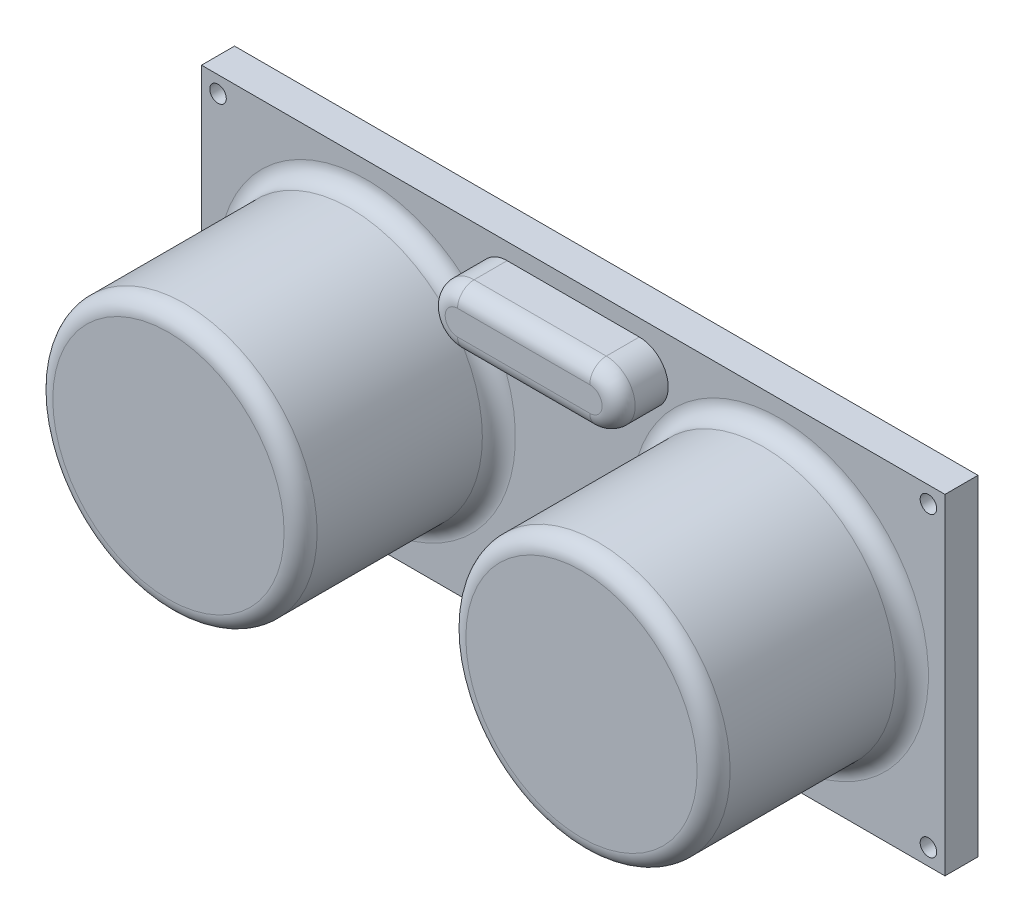
SolidWorks part; units mm, degrees
ref_plane "Alzado" through (0, 0, 0) normal (0, 0, 1) x (1, 0, 0)
ref_plane "Planta" through (0, 0, 0) normal (0, 1, 0) x (1, 0, 0)
ref_plane "Vista lateral" through (0, 0, 0) normal (1, 0, 0) x (0, 0, -1)
sketch "Croquis1" plane through (0, 0, 0) normal (0, 0, 1) x (1, 0, 0)
  line L1 (-22.5, -10) -> (22.5, -10)
  line L2 (-22.5, -10) -> (-22.5, 10)
  line L3 (-22.5, 10) -> (22.5, 10)
  line L4 (22.5, -10) -> (22.5, 10)
  line L5 (-22.5, -10) -> (22.5, 10) construction
  line L6 (-22.5, 10) -> (22.5, -10) construction
  point P0 (0, 0)
extrude "Saliente-Extruir1" add sketch "Croquis1" along normal blind 2
sketch "Croquis2" plane through (0, 0, 2) normal (0, 0, 1) x (1, 0, 0)
  line L0 (-22.5, 0) -> (22.5, 0) construction
  line L1 (-22.5, 10) -> (-22.5, -10) construction
  line L2 (22.5, -10) -> (22.5, 10) construction
  line L3 (22.5, 0) -> (20.5, 0) construction
  line L4 (20.5, 0) -> (12.5, 0) construction
  line L5 (0, 0) -> (0, 10) construction
  line L6 (22.5, 10) -> (-22.5, 10) construction
  circle A0 centre (12.5, 0) radius 8
  circle A1 centre (-12.5, 0) radius 8
extrude "Saliente-Extruir2" add sketch "Croquis2" along normal blind 12
fillet "Redondeo1" radius 1 4 edges at (-20.5, 0, 2) (-20.5, 0, 14) (4.5, 0, 2) (20.5, 0, 14)
sketch "Croquis3" plane through (0, 0, 2) normal (0, 0, 1) x (1, 0, 0)
  line L0 (0, 0) -> (0, 10) construction
  line L1 (22.5, 10) -> (-22.5, 10) construction
  line L2 (0, 10) -> (0, 9) construction
  line L3 (0, 9) -> (0, 5.5) construction
  line L4 (0, 5.5) -> (0, 7.25) construction
  line L5 (0, 7.25) -> (4, 7.25) construction
  line L6 (4, 7.25) -> (-4, 7.25) construction
  line L8 (4, 5.5) -> (-4, 5.5)
  line L9 (4, 9) -> (-4, 9)
  arc A0 (4, 5.5) -> (4, 9) centre (4, 7.25) ccw
  arc A1 (-4, 9) -> (-4, 5.5) centre (-4, 7.25) ccw
  point P12 (0, 7.25)
extrude "Saliente-Extruir3" add sketch "Croquis3" along normal blind 3
fillet "Redondeo2" radius 1 4 edges at (0, 5.5, 5) (-5.75, 7.25, 5) (0, 9, 5) (5.75, 7.25, 5)
sketch "Croquis4" plane through (0, 0, 2) normal (0, 0, 1) x (1, 0, 0)
  line L0 (0, 0) -> (0, 50000) construction
  line L1 (0, 0) -> (50000, 0) construction
  line L2 (22.5, 10) -> (22.5, 9) construction
  line L3 (22.5, -10) -> (22.5, 10) construction
  line L4 (22.5, 9) -> (21.5, 9) construction
  circle A0 centre (21.5, 9) radius 0.5
  circle A1 centre (21.5, -9) radius 0.5
  circle A2 centre (-21.5, -9) radius 0.5
  circle A3 centre (-21.5, 9) radius 0.5
extrude "Cortar-Extruir1" cut sketch "Croquis4" against normal through all
sketch "Croquis5" plane through (0, 0, 0) normal (0, 0, -1) x (-1, 0, 0)
  line L0 (0, 0) -> (0, -10) construction
  line L1 (22.5, -10) -> (-22.5, -10) construction
  line L2 (0, -10) -> (0, -7) construction
  line L3 (-5, -7) -> (5, -7) construction
  line L5 (5, -7) -> (-5, -7)
  line L6 (5, -7) -> (5, -10)
  line L7 (5, -10) -> (-5, -10)
  line L8 (-5, -7) -> (-5, -10)
  point P9 (0, -7)
extrude "Saliente-Extruir4" add sketch "Croquis5" along normal blind 2.54
chamfer "Chaflán1" distance 0.2 angle 45 4 edges at (-5, -10, -1.27) (-5, -7, -1.27) (5, -10, -1.27) (5, -7, -1.27)
sketch "Croquis6" plane through (0, 0, -2.54) normal (0, 0, -1) x (-1, 0, 0)
  line L0 (0, -7) -> (0, -10) construction
  line L1 (4.8, -7) -> (-4.8, -7) construction
  line L2 (-4.8, -10) -> (4.8, -10) construction
  line L3 (0, -10) -> (0, -8.5) construction
  line L4 (0, -8.5) -> (5, -8.5) construction
  line L5 (5, -9.8) -> (5, -7.2) construction
  line L6 (5, -8.5) -> (-5, -8.5) construction
  line L7 (-5, -7.2) -> (-5, -9.8) construction
  line L8 (-5, -8.5) -> (0, -8.5) construction
  line L9 (0, -8.5) -> (-2.5, -8.5) construction
  line L10 (-2.5, -8.5) -> (-5, -8.5) construction
  line L11 (-5, -8.5) -> (-3.75, -8.5) construction
  line L12 (-3.75, -8.5) -> (-1.25, -8.5) construction
  line L13 (5, -8.5) -> (0, -8.5) construction
  line L14 (0, -8.5) -> (2.5, -8.5) construction
  line L15 (2.5, -8.5) -> (1.25, -8.5) construction
  line L16 (1.25, -8.5) -> (2.5, -8.5) construction
  line L17 (2.5, -8.5) -> (5, -8.5) construction
  line L18 (5, -8.5) -> (3.75, -8.5) construction
  line L20 (-4.1, -8.85) -> (-3.4, -8.85)
  line L21 (-4.1, -8.85) -> (-4.1, -8.15)
  line L22 (-4.1, -8.15) -> (-3.4, -8.15)
  line L23 (-3.4, -8.85) -> (-3.4, -8.15)
  line L24 (-4.1, -8.85) -> (-3.4, -8.15) construction
  line L25 (-4.1, -8.15) -> (-3.4, -8.85) construction
  line L26 (-1.6, -8.85) -> (-0.9, -8.85)
  line L27 (-1.6, -8.85) -> (-1.6, -8.15)
  line L28 (-1.6, -8.15) -> (-0.9, -8.15)
  line L29 (-0.9, -8.85) -> (-0.9, -8.15)
  line L30 (-1.6, -8.85) -> (-0.9, -8.15) construction
  line L31 (-1.6, -8.15) -> (-0.9, -8.85) construction
  line L32 (0.9, -8.85) -> (1.6, -8.85)
  line L33 (0.9, -8.85) -> (0.9, -8.15)
  line L34 (0.9, -8.15) -> (1.6, -8.15)
  line L35 (1.6, -8.85) -> (1.6, -8.15)
  line L36 (0.9, -8.85) -> (1.6, -8.15) construction
  line L37 (0.9, -8.15) -> (1.6, -8.85) construction
  line L38 (3.4, -8.85) -> (4.1, -8.85)
  line L39 (3.4, -8.85) -> (3.4, -8.15)
  line L40 (3.4, -8.15) -> (4.1, -8.15)
  line L41 (4.1, -8.85) -> (4.1, -8.15)
  line L42 (3.4, -8.85) -> (4.1, -8.15) construction
  line L43 (3.4, -8.15) -> (4.1, -8.85) construction
extrude "Saliente-Extruir5" add sketch "Croquis6" along normal blind 1
sketch "Croquis7" plane through (0, 0, -3.54) normal (0, 0, -1) x (-1, 0, 0)
  line L0 (-4.1, -8.85) -> (4.1, -8.85) construction
  line L1 (-4.1, -8.85) -> (-4.1, -9.15) construction
  line L2 (-4.1, -9.15) -> (4.1, -9.15) construction
  line L4 (-4.1, -8.15) -> (-3.4, -8.15)
  line L5 (-4.1, -8.15) -> (-4.1, -8.85)
  line L6 (-4.1, -8.85) -> (-3.4, -8.85)
  line L7 (-3.4, -8.15) -> (-3.4, -8.85)
  line L8 (-1.6, -8.15) -> (-0.9, -8.15)
  line L9 (-1.6, -8.15) -> (-1.6, -8.85)
  line L10 (-1.6, -8.85) -> (-0.9, -8.85)
  line L11 (-0.9, -8.15) -> (-0.9, -8.85)
  line L12 (0.9, -8.15) -> (1.6, -8.15)
  line L13 (0.9, -8.15) -> (0.9, -8.85)
  line L14 (0.9, -8.85) -> (1.6, -8.85)
  line L15 (1.6, -8.15) -> (1.6, -8.85)
  line L16 (3.4, -8.15) -> (4.1, -8.15)
  line L17 (3.4, -8.15) -> (3.4, -8.85)
  line L18 (3.4, -8.85) -> (4.1, -8.85)
  line L19 (4.1, -8.15) -> (4.1, -8.85)
revolve "Revolución1" add sketch "Croquis7" angle 90 about L2
sketch "Croquis8" plane through (0, -9.15, 0) normal (0, -1, 0) x (1, 0, 0)
  line L0 (3.4, -3.84) -> (3.4, -4.54) construction
  line L1 (4.1, -3.84) -> (3.4, -3.84)
  line L2 (4.1, -3.84) -> (4.1, -4.54)
  line L3 (4.1, -4.54) -> (3.4, -4.54)
  line L4 (3.4, -3.84) -> (3.4, -4.54)
  line L5 (-4.1, -4.54) -> (-3.4, -4.54) construction
  line L6 (1.6, -3.84) -> (0.9, -3.84)
  line L7 (1.6, -3.84) -> (1.6, -4.54)
  line L8 (1.6, -4.54) -> (0.9, -4.54)
  line L9 (0.9, -3.84) -> (0.9, -4.54)
  line L10 (-0.9, -3.84) -> (-1.6, -3.84)
  line L11 (-0.9, -3.84) -> (-0.9, -4.54)
  line L12 (-0.9, -4.54) -> (-1.6, -4.54)
  line L13 (-1.6, -3.84) -> (-1.6, -4.54)
  line L14 (-3.4, -3.84) -> (-4.1, -3.84)
  line L15 (-3.4, -3.84) -> (-3.4, -4.54)
  line L16 (-3.4, -4.54) -> (-4.1, -4.54)
  line L17 (-4.1, -3.84) -> (-4.1, -4.54)
extrude "Saliente-Extruir6" add sketch "Croquis8" along normal blind 6
